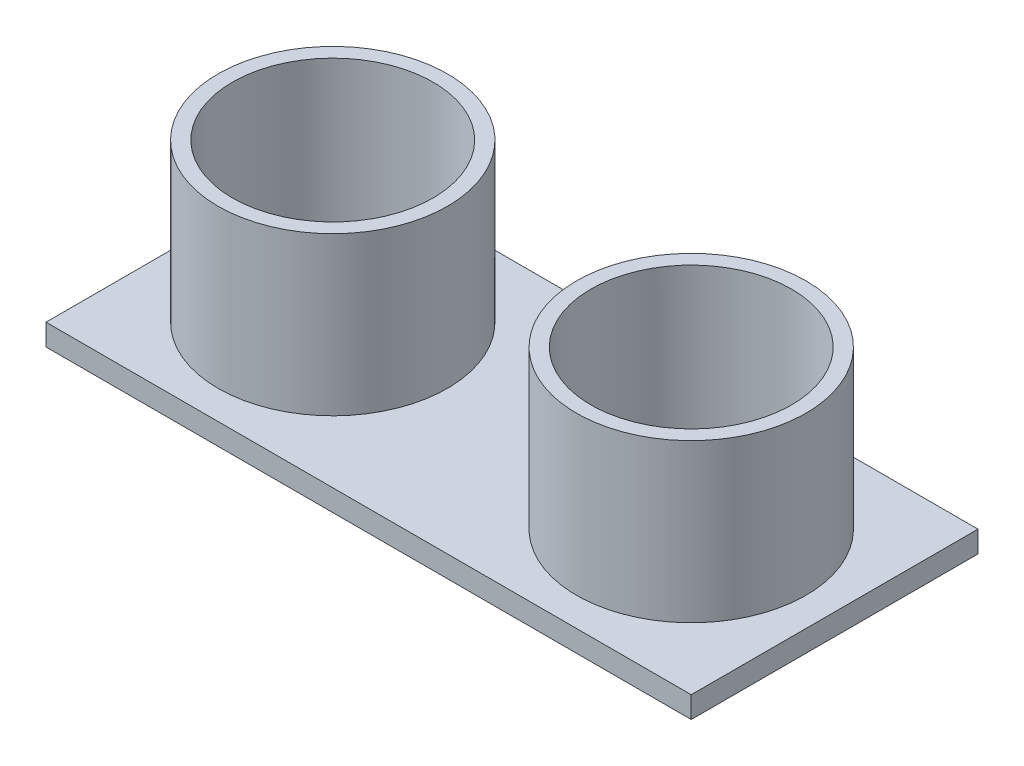
SolidWorks part; units mm, degrees
ref_plane "Front Plane" through (0, 0, 0) normal (0, 0, 1) x (1, 0, 0)
ref_plane "Top Plane" through (0, 0, 0) normal (0, 1, 0) x (1, 0, 0)
ref_plane "Right Plane" through (0, 0, 0) normal (1, 0, 0) x (0, 0, -1)
sketch "Sketch1" plane through (0, 0, 0) normal (0, 1, 0) x (1, 0, 0)
  line L1 (22.5, -10) -> (-22.5, -10)
  line L2 (22.5, -10) -> (22.5, 10)
  line L3 (22.5, 10) -> (-22.5, 10)
  line L4 (-22.5, -10) -> (-22.5, 10)
  line L5 (22.5, -10) -> (-22.5, 10) construction
  line L6 (22.5, 10) -> (-22.5, -10) construction
  point P0 (0, 0)
  dimension "D1" = 20
  dimension "D2" = 45
extrude "Boss-Extrude1" add sketch "Sketch1" along normal blind 1.5
sketch "Sketch3" plane through (0, 1.5, 0) normal (0, 1, 0) x (1, 0, 0)
  line L0 (22.5, 10) -> (-22.5, 10) construction
  line L1 (-22.5, 10) -> (-22.5, -10) construction
  line L2 (0, -10) -> (0, 10) construction
  line L3 (-22.5, -10) -> (22.5, -10) construction
  circle A0 centre (-12.5, 0) radius 8
  circle A1 centre (-12.5, 0) radius 7
  circle A2 centre (12.5, 0) radius 7
  circle A3 centre (12.5, 0) radius 8
  dimension "D1" = 16
  dimension "D4" = 14
  dimension "D2" = 10
  dimension "D3" = 10
extrude "Boss-Extrude2" add sketch "Sketch3" along normal blind 11
